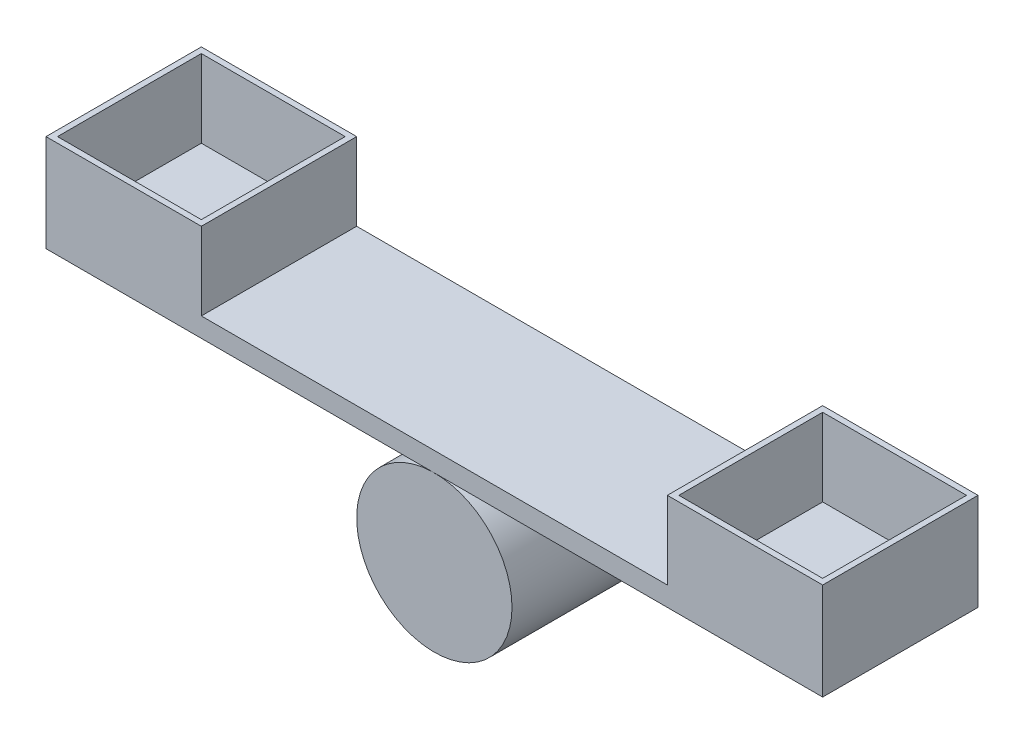
SolidWorks part; units mm, degrees
ref_plane "Front Plane" through (0, 0, 0) normal (0, 0, 1) x (1, 0, 0)
ref_plane "Top Plane" through (0, 0, 0) normal (0, 1, 0) x (1, 0, 0)
ref_plane "Right Plane" through (0, 0, 0) normal (1, 0, 0) x (0, 0, -1)
sketch "Sketch1" plane through (0, 0, 0) normal (0, 0, 1) x (1, 0, 0)
  line L0 (0, 50.8) -> (254, 50.8)
  line L1 (254, 50.8) -> (254, 63.5)
  line L2 (254, 63.5) -> (-254, 63.5)
  line L3 (-254, 63.5) -> (-254, 50.8)
  line L4 (-254, 50.8) -> (0, 50.8)
  circle A0 centre (0, 0) radius 50.8
extrude "Boss-Extrude1" add sketch "Sketch1" along normal blind 101.6 contours L3 L4 L0 L1 L2 | A0
sketch "Sketch2" plane through (0, 63.5, 0) normal (0, 1, 0) x (1, 0, 0)
  line L0 (-254, 0) -> (-152.4, 0)
  line L1 (254, 0) -> (-254, 0) construction
  line L2 (-152.4, 0) -> (-152.4, -101.6)
  line L3 (254, -101.6) -> (-254, -101.6) construction
  line L4 (-152.4, -101.6) -> (-254, -101.6)
  line L5 (-254, -101.6) -> (-254, 0) construction
  line L6 (-254, -101.6) -> (-254, 0)
  line L7 (254, 0) -> (254, -101.6)
  line L8 (254, -101.6) -> (152.4, -101.6)
  line L9 (152.4, -101.6) -> (152.4, 0)
  line L10 (152.4, 0) -> (254, 0)
  line L12 (-250.2427, -3.7573) -> (-156.1573, -3.7573)
  line L13 (-156.1573, -3.7573) -> (-156.1573, -97.8427)
  line L14 (-156.1573, -97.8427) -> (-250.2427, -97.8427)
  line L15 (-250.2427, -97.8427) -> (-250.2427, -3.7573)
  line L16 (250.2427, -3.7573) -> (250.2427, -97.8427)
  line L17 (250.2427, -97.8427) -> (156.1573, -97.8427)
  line L18 (156.1573, -97.8427) -> (156.1573, -3.7573)
  line L19 (156.1573, -3.7573) -> (250.2427, -3.7573)
extrude "Boss-Extrude2" add sketch "Sketch2" along normal blind 50.8
